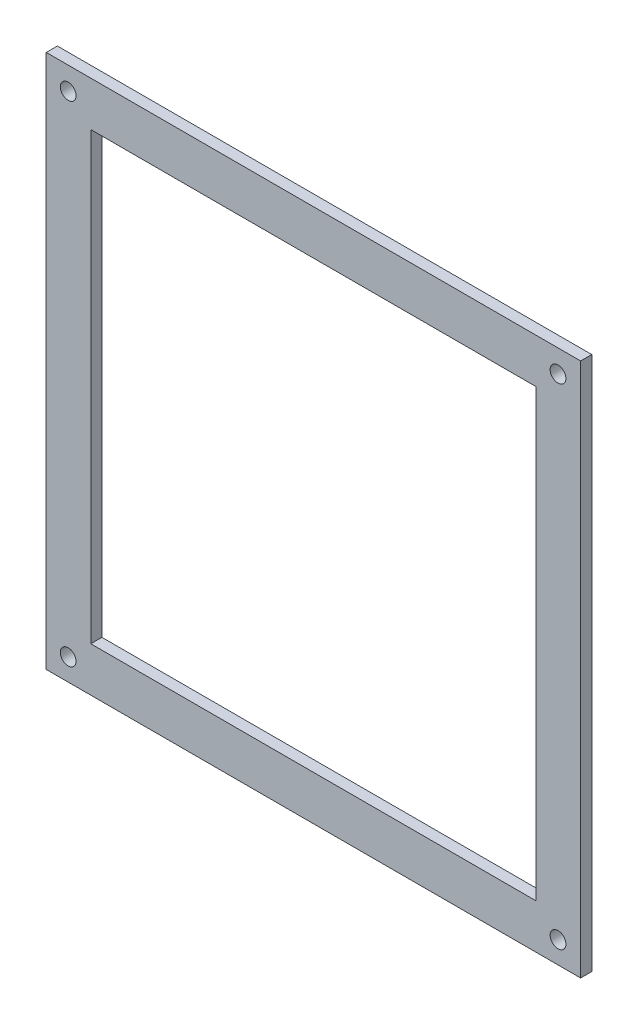
SolidWorks part; units mm, degrees
ref_plane "Front Plane" through (0, 0, 0) normal (0, 0, 1) x (1, 0, 0)
ref_plane "Top Plane" through (0, 0, 0) normal (0, 1, 0) x (1, 0, 0)
ref_plane "Right Plane" through (0, 0, 0) normal (1, 0, 0) x (0, 0, -1)
sketch "Sketch1" plane through (0, 0, 0) normal (0, 0, 1) x (1, 0, 0)
  line L1 (-37.8687, 40.7283) -> (114.5313, 40.7283)
  line L2 (-37.8687, 40.7283) -> (-37.8687, -111.6717)
  line L3 (-37.8687, -111.6717) -> (114.5313, -111.6717)
  line L4 (114.5313, 40.7283) -> (114.5313, -111.6717)
  line L5 (-25.1687, 28.0283) -> (101.8313, 28.0283)
  line L6 (-25.1687, 28.0283) -> (-25.1687, -98.9717)
  line L7 (-25.1687, -98.9717) -> (101.8313, -98.9717)
  line L8 (101.8313, 28.0283) -> (101.8313, -98.9717)
  dimension "D1" = 152.4
  dimension "D2" = 12.7
  dimension "D3" = 12.7
  dimension "D4" = 12.7
  dimension "D5" = 12.7
extrude "Boss-Extrude1" add sketch "Sketch1" along normal blind 3.175
hole_wizard "#8 Clearance Hole2" positions "Sketch2" profile "Sketch3" hole size "#8" standard "ANSI Inch" end condition through all
sketch "Sketch2" plane through (0, 0, 3.175) normal (0, 0, 1) x (1, 0, 0)
  line L0 (-37.8687, 29.6239) -> (-31.6161, 29.6239)
  line L1 (-37.8687, 40.7283) -> (-37.8687, -111.6717) construction
  line L3 (-31.6161, 40.7283) -> (-31.6161, 34.2736)
  line L4 (114.5313, 40.7283) -> (-37.8687, 40.7283) construction
  point P8 (-31.6161, 34.2736)
sketch "Sketch3" plane through (-31.6161, 34.2736, 3.175) normal (1, 0, 0) x (0, -1, 0)
  line L0 (0, 0) -> (0, 3.175)
  line L1 (0, 3.175) -> (2.2479, 3.175)
  line L2 (2.2479, 3.175) -> (2.2479, 0)
  line L5 (2.2479, 0) -> (0, 0)
  line L11 (0, -6.35) -> (0, 107.95) construction
  dimension "Thru Hole Dia." = 4.4958
  dimension "Thru Hole Depth" = 3.175
pattern_linear "LPattern1" count 2 spacing 139.7 along (1, 0, 0) count 2 spacing 139.7 along (0, -1, 0) of "#8 Clearance Hole2"
